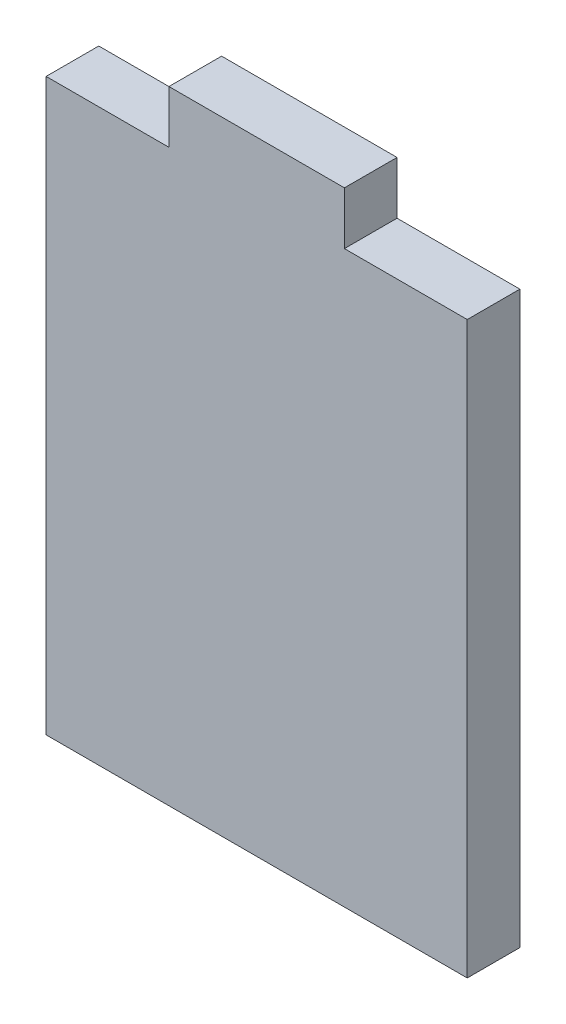
SolidWorks part; units mm, degrees
ref_plane "Plan de face" through (0, 0, 0) normal (0, 0, 1) x (1, 0, 0)
ref_plane "Plan de dessus" through (0, 0, 0) normal (0, 1, 0) x (1, 0, 0)
ref_plane "Plan de droite" through (0, 0, 0) normal (1, 0, 0) x (0, 0, -1)
sketch "Esquisse1" plane through (0, 0, 0) normal (0, 0, 1) x (1, 0, 0)
  line L1 (-53.4278, 35.3167) -> (-5.4278, 35.3167)
  line L2 (-53.4278, 35.3167) -> (-53.4278, -29.6833)
  line L3 (-53.4278, -29.6833) -> (-5.4278, -29.6833)
  line L4 (-5.4278, 35.3167) -> (-5.4278, -29.6833)
  dimension "D1" = 65
  dimension "D2" = 48
extrude "Boss.-Extru.1" add sketch "Esquisse1" along normal blind 6
sketch "Esquisse3" plane through (0, 0, 6) normal (0, 0, 1) x (1, 0, 0)
  line L0 (-5.4278, 35.3167) -> (-53.4278, 35.3167) construction
  line L1 (-39.4278, 35.3167) -> (-19.4278, 35.3167)
  line L2 (-39.4278, 35.3167) -> (-39.4278, 41.3167)
  line L3 (-39.4278, 41.3167) -> (-19.4278, 41.3167)
  line L4 (-19.4278, 35.3167) -> (-19.4278, 41.3167)
  line L5 (-5.4278, -29.6833) -> (-5.4278, 35.3167) construction
  dimension "D1" = 6
  dimension "D2" = 20
  dimension "D3" = 14
extrude "Boss.-Extru.2" add sketch "Esquisse3" against normal blind 6
